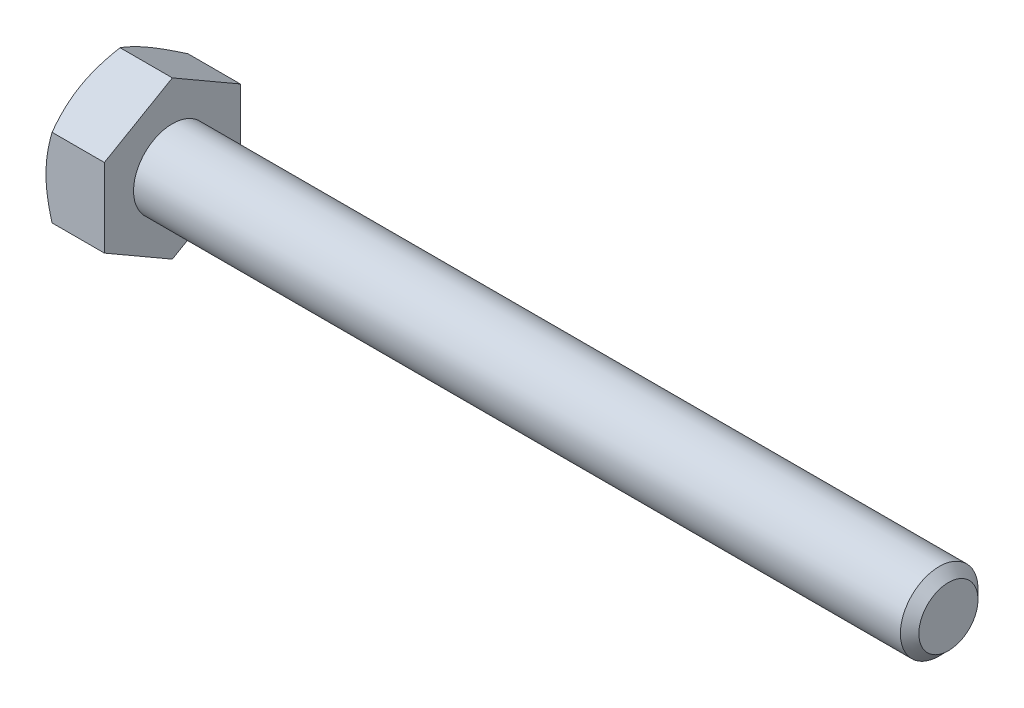
SolidWorks part; units mm, degrees
extrude "BaseHead" add sketch "Sketch1" along normal blind 4.7752
sketch "Sketch1" plane through (0, 0, 0) normal (1, 0, 0) x (0, 0, -1)
  line L0 (5.5626, 3.2116) -> (5.5626, -3.2116)
  line L1 (-5.5626, 3.2116) -> (-5.5626, -3.2116)
  line L2 (5.5626, -3.2116) -> (0, -6.4231)
  line L3 (0, -6.4231) -> (-5.5626, -3.2116)
  line L4 (5.5626, 3.2116) -> (0, 6.4231)
  line L5 (0, 6.4231) -> (-5.5626, 3.2116)
  dimension "Width_flats" = 11.1252
  dimension "D2" = 120
  dimension "D3" = 5.5626
  dimension "D4" = 5.5626
  dimension "D5" = 5.5626
ref_plane "Plane1" through (0, 0, 0) normal (0, 0, 1) x (1, 0, 0)
ref_plane "Plane2" through (0, 0, 0) normal (0, 1, 0) x (1, 0, 0)
ref_plane "Plane3" through (0, 0, 0) normal (1, 0, 0) x (0, 0, -1)
sketch "BodySke" plane through (0, 0, 0) normal (0, 0, 1) x (1, 0, 0)
  line L0 (0, 3.2116) -> (0, -3.2116) construction
  line L1 (0, 0) -> (68.2752, 0)
  line L2 (0, 0) -> (0, 3.175)
  line L3 (0, 3.175) -> (67.5195, 3.175)
  line L4 (68.2752, 0) -> (68.2752, 2.4193)
  line L5 (4.7752, 6.4231) -> (4.7752, 3.2116) construction
  line L6 (68.2752, 2.4193) -> (67.5195, 3.175)
  line L7 (0, 0) -> (96.52, 0) construction
  line L8 (68.2752, -2.4193) -> (67.5195, -3.175) construction
  line L9 (0, -3.175) -> (67.5195, -3.175) construction
  line L10 (6.0452, 15.24) -> (6.0452, -2.54) construction
  line L11 (49.2252, 15.24) -> (49.2252, -2.54) construction
  line L12 (4.7752, 3.2116) -> (4.7752, -3.2116) construction
  dimension "Diameter" = 6.35
  dimension "Advance" = 1.27
revolve "BaseBody" add sketch "BodySke" angle 360 about L7
cosmetic thread "ThreadCosmetic" [suppressed] parameters "Thread_length"=19.05, "Thread_minor"=4.8387
sketch "Sketch3" plane through (0, 0, 0) normal (0, 0, 1) x (1, 0, 0)
  line L0 (0, 5.5626) -> (4.163, 12.7731)
  line L1 (0, 6.4231) -> (0, 3.2116) construction
  line L2 (4.163, 12.7731) -> (4.163, 19.1231)
  line L3 (4.163, 19.1231) -> (-12.7, 19.1231)
  line L4 (-12.7, 19.1231) -> (-12.7, 5.5626)
  line L5 (-12.7, 5.5626) -> (0, 5.5626)
  line L6 (0, 0) -> (99.06, 0) construction
  line L7 (4.7752, 6.4231) -> (0, 6.4231) construction
  dimension "D1" = 5.5626
  dimension "D2" = 6.35
  dimension "D3" = 12.7
  dimension "D4" = 6.35
  dimension "Head_ch_ang" = 30
revolve "HeadChamfer" cut sketch "Sketch3" angle 360 about L6
fillet "HeadFillet" [suppressed] radius 0.762
sketch "ThdSchSke" plane through (0, 0, 0) normal (0, 0, 1) x (1, 0, 0)
  line L0 (49.2252, -2.4193) -> (48.6961, -3.175)
  line L1 (49.2252, -2.4193) -> (49.7543, -3.175)
  line L2 (49.7543, -3.175) -> (49.7543, -3.9687)
  line L3 (-3.175, 0) -> (5.1513, 0) construction
  line L5 (49.7543, -3.9687) -> (48.6961, -3.9687)
  line L6 (48.6961, -3.9687) -> (48.6961, -3.175)
  dimension "Thread_minor" = 4.8387
  dimension "Diameter" = 6.35
revolve "ThreadSchematic" [suppressed] cut sketch "ThdSchSke" angle 360 about L3
pattern_linear "ThdSchPat" [suppressed]
equation "\"D3@Sketch1\" = \"Width_flats@Sketch1\" / 2"
equation "\"D4@Sketch1\" = \"D3@Sketch1\""
equation "\"D5@Sketch1\" = \"D4@Sketch1\""
equation "\"Thread_minor@ThreadCosmetic\" = \"Minor_dia@BodySke\""
equation "\"D1@Sketch3\" = \"Width_flats@Sketch1\" / 2"
equation "\"Thread_length@ThreadCosmetic\" = ((sgn( (\"Length@BodySke\" - \"Advance@BodySke\" ) - \"Thread_nom@BodySke\" )-1)*( (\"Length@BodySke\" - \"Advance@BodySke\" ) - \"Thread_nom@BodySke\" ))/-2+ \"Thread_nom@BodySke\""
equation "\"Thread_minor@ThdSchSke\" = \"Minor_dia@BodySke\""
equation "\"Diameter@ThdSchSke\" = \"Diameter@BodySke\""
equation "\"Overcut@ThdSchSke\" = \"Diameter@BodySke\" * 1.25"
equation "\"Start@ThdSchSke\" = \"Head_ht@BaseHead\" + \"Length@BodySke\" - \"Thread_length@ThreadCosmetic\"  '---Non-countersunk---"
equation "\"Num_threads@ThdSchPat\" = int( \"Thread_length@ThreadCosmetic\" / \"Advance@BodySke\" + 0.999 )  + 1"
equation "\"Advance@ThdSchPat\" = \"Thread_length@ThreadCosmetic\" /  (\"Num_threads@ThdSchPat\" - 1) 'relax it"
equation "\"Num_threads@ThdSchPat\" = \"Num_threads@ThdSchPat\" - sgn( \"Num_threads@ThdSchPat\" - 1) '---chamfered tips only---"
